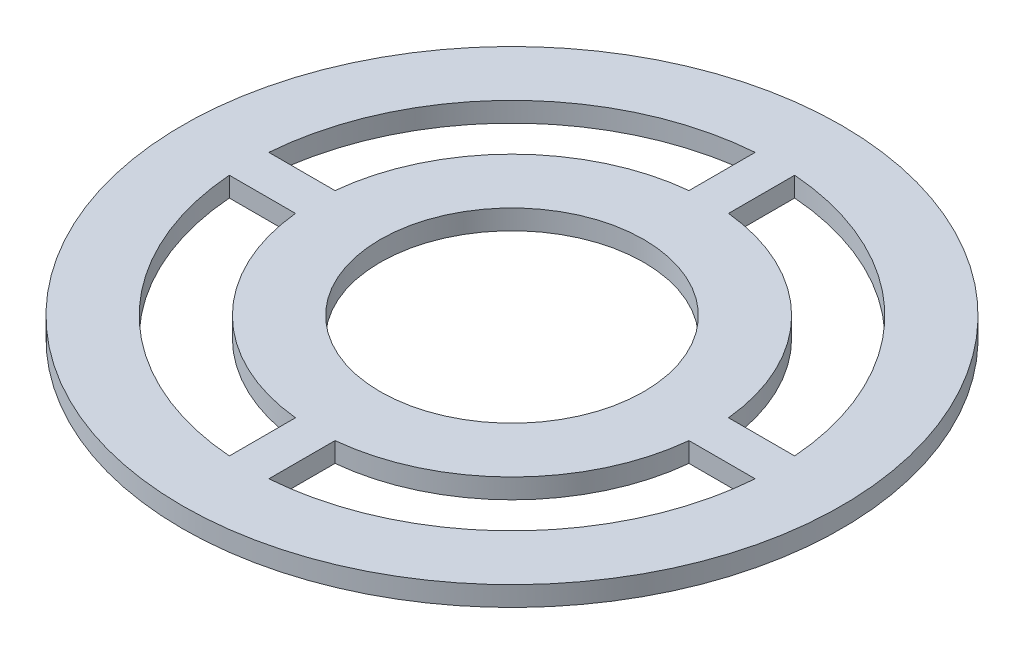
SolidWorks part; units mm, degrees
ref_plane "Plan de face" through (0, 0, 0) normal (0, 0, 1) x (1, 0, 0)
ref_plane "Plan de dessus" through (0, 0, 0) normal (0, 1, 0) x (1, 0, 0)
ref_plane "Plan de droite" through (0, 0, 0) normal (1, 0, 0) x (0, 0, -1)
sketch "Esquisse1" plane through (0, 0, 0) normal (0, 1, 0) x (1, 0, 0)
  circle A0 centre (0, 0) radius 10
  circle A1 centre (0, 0) radius 20
  circle A2 centre (0, 0) radius 25
  circle A3 centre (0, 0) radius 15
extrude "Boss.-Extru.3" add sketch "Esquisse1" along normal blind 1.5 contours A2 A1 | A3 A0
sketch "Esquisse3" plane through (0, 1.5, 0) normal (0, 1, 0) x (-1, 0, 0)
  line L1 (21.9248, -1.5) -> (14.9248, -1.5)
  line L2 (21.9248, -1.5) -> (21.9248, 1.5)
  line L3 (21.9248, 1.5) -> (14.9248, 1.5)
  line L4 (14.9248, -1.5) -> (14.9248, 1.5)
  line L5 (1.5, -21) -> (-1.5, -21)
  line L6 (1.5, -21) -> (1.5, -14)
  line L7 (1.5, -14) -> (-1.5, -14)
  line L8 (-1.5, -21) -> (-1.5, -14)
  line L9 (-14, -1.5) -> (-21, -1.5)
  line L10 (-14, -1.5) -> (-14, 1.5)
  line L11 (-14, 1.5) -> (-21, 1.5)
  line L12 (-21, -1.5) -> (-21, 1.5)
  line L13 (1.5, 14) -> (-1.5, 14)
  line L14 (1.5, 14) -> (1.5, 21)
  line L15 (1.5, 21) -> (-1.5, 21)
  line L16 (-1.5, 14) -> (-1.5, 21)
  circle A0 centre (0, 0) radius 15 construction
  dimension "D1" = 7
  dimension "D2" = 7
  dimension "D3" = 7
  dimension "D4" = 3
  dimension "D5" = 7
  dimension "D6" = 3
  dimension "D7" = 3
  dimension "D8" = 3
  dimension "D9" = 14
  dimension "D10" = 14
  dimension "D11" = 14
  dimension "D12" = 1.5
  dimension "D13" = 1.5
  dimension "D14" = 1.5
  dimension "D15" = 1.5
extrude "Boss.-Extru.5" add sketch "Esquisse3" against normal blind 1.5
